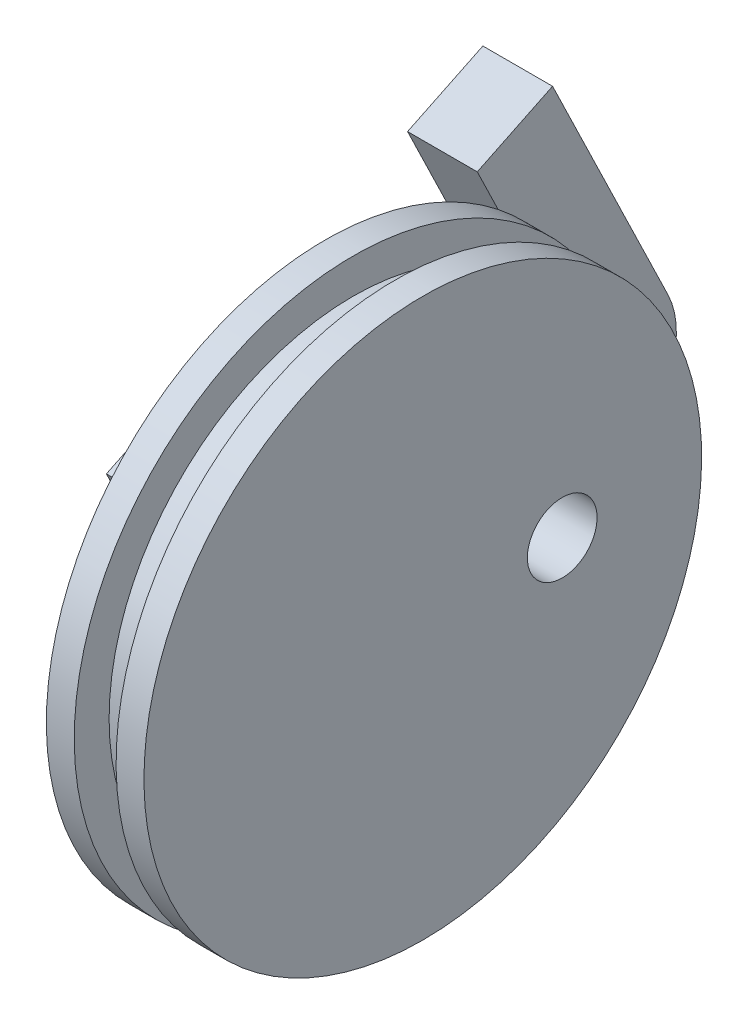
SolidWorks part; units mm, degrees
ref_plane "Front Plane" through (0, 0, 0) normal (0, 0, 1) x (1, 0, 0)
ref_plane "Top Plane" through (0, 0, 0) normal (0, 1, 0) x (1, 0, 0)
ref_plane "Right Plane" through (0, 0, 0) normal (1, 0, 0) x (0, 0, -1)
sketch "Sketch1" plane through (0, 0, 0) normal (0, 0, 1) x (1, 0, 0)
  line L0 (0, 20) -> (0, -4.1034) construction
  line L1 (-3.5, 0) -> (3.5, 0)
  line L2 (-3.5, 0) -> (-3.5, 20)
  line L3 (-3.5, 20) -> (3.5, 20)
  line L4 (3.5, 0) -> (3.5, 20)
  line L5 (-3.5, 0) -> (3.5, 20) construction
  line L6 (-3.5, 20) -> (3.5, 0) construction
  line L7 (-1.5, 22.5) -> (1.5, 22.5)
  line L8 (-1.5, 22.5) -> (-1.5, 17.5)
  line L9 (-1.5, 17.5) -> (1.5, 17.5)
  line L10 (1.5, 22.5) -> (1.5, 17.5)
  line L11 (-1.5, 22.5) -> (1.5, 17.5) construction
  line L12 (-1.5, 17.5) -> (1.5, 22.5) construction
  point P0 (0, 0)
  point P6 (0, 20)
  point P13 (0, 0)
  point P14 (3.5, -1.0607)
  dimension "D1" = 7
  dimension "D2" = 3
  dimension "D3" = 20
  dimension "D4" = 17.5
revolve "Revolve1" add sketch "Sketch1" angle 360 about L1
sketch "Sketch3" plane through (-3.5, 0, 0) normal (-1, 0, 0) x (0, 0, 1)
  line L0 (-10.9078, 18.773) -> (-19.1897, 1.673)
  line L2 (-19.1897, 1.673) -> (-2.9897, -6.173)
  line L3 (5.2922, 10.927) -> (-2.9897, -6.173)
  line L4 (0, 0) -> (-10, 0) construction
  line L5 (-16.3078, 21.3883) -> (-24.5897, 4.2883)
  line L6 (-21.8051, -3.727) -> (-5.6051, -11.573)
  line L7 (10.6922, 8.3117) -> (2.4103, -8.7883)
  line L9 (-10.9078, 18.773) -> (-16.3078, 21.3883)
  line L10 (-16.3078, 21.3883) -> (-10.9078, 18.773)
  line L11 (-13.6925, 26.7883) -> (-27.2051, -1.1117) construction
  line L12 (-13.6925, 26.7883) -> (13.3075, 13.7117) construction
  line L13 (13.3075, 13.7117) -> (-0.2051, -14.1883) construction
  line L14 (5.2922, 10.927) -> (10.6922, 8.3117)
  line L15 (-10.9078, 18.773) -> (5.2922, 10.927) construction
  line L16 (-27.2051, -1.1117) -> (-0.2051, -14.1883) construction
  circle A0 centre (-10, 0) radius 2.5 construction
  arc A1 (-24.5897, 4.2883) -> (-21.8051, -3.727) centre (-19.1897, 1.673) ccw
  arc A2 (-5.6051, -11.573) -> (2.4103, -8.7883) centre (-2.9897, -6.173) ccw
  point P8 (0, 0)
  circle M5 centre (0, 0) radius 20
  dimension "D4" = 5
  dimension "D7" = 6
  dimension "D1" = 18
  dimension "D2" = 19
  dimension "D3" = 10
  dimension "D5" = 9
  dimension "D6" = 6
extrude "Boss-Extrude1" add sketch "Sketch3" along normal blind 5 contours L6 A2 L7 L14 L3 L2 L0 M5 | L5 A1 L6 L0 L9 M5
sketch "Sketch4" plane through (-3.5, 0, 0) normal (-1, 0, 0) x (0, 0, 1)
  line L0 (-19.1897, 1.673) -> (-2.9897, -6.173) construction
  circle A0 centre (-10, 0) radius 2.5
  point P4 (0, 0)
  dimension "D1" = 5
extrude "Cut-Extrude1" cut sketch "Sketch4" against normal through all
